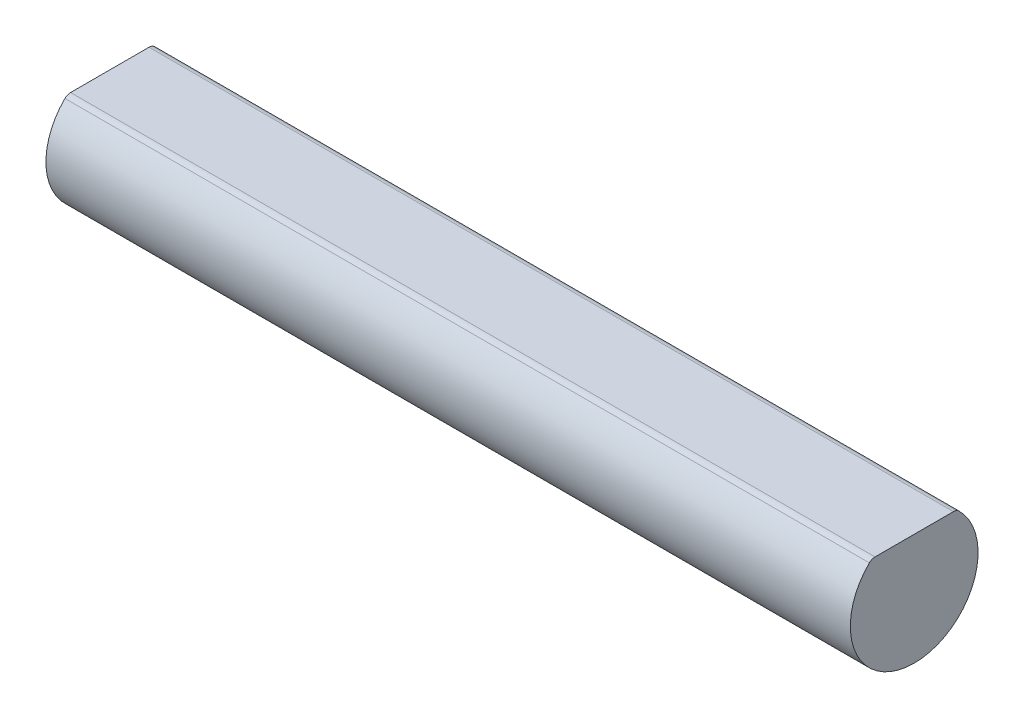
SolidWorks part; units mm, degrees
ref_plane "Front Plane" through (0, 0, 0) normal (0, 0, 1) x (1, 0, 0)
ref_plane "Top Plane" through (0, 0, 0) normal (0, 1, 0) x (1, 0, 0)
ref_plane "Right Plane" through (0, 0, 0) normal (1, 0, 0) x (0, 0, -1)
sketch "Sketch1" plane through (0, 0, 0) normal (1, 0, 0) x (0, 0, -1)
  circle A0 centre (0, 0) radius 7.94
  dimension "D1" = 15.88
extrude "Boss-Extrude1" add sketch "Sketch1" along normal blind 100
sketch "Sketch2" plane through (100, 0, 0) normal (1, 0, 0) x (0, 0, -1)
  line L0 (0, 8.734) -> (0, -8.734) construction
  line L2 (0, 5.94) -> (-10.6918, 5.94)
  line L3 (0, 5.94) -> (0, 9.217)
  line L4 (0, 9.217) -> (-10.6918, 9.217)
  line L5 (-10.6918, 5.94) -> (-10.6918, 9.217)
  line L6 (0, 5.94) -> (8.9119, 5.94)
  line L7 (0, 5.94) -> (0, 9.217)
  line L8 (0, 9.217) -> (8.9119, 9.217)
  line L9 (8.9119, 5.94) -> (8.9119, 9.217)
  circle A0 centre (0, 0) radius 7.94 construction
  point P0 (0, 7.94)
  point P1 (0, 5.94)
  circle M1 centre (0, 0) radius 7.94
  dimension "D1" = 2
extrude "Cut-Extrude1" cut sketch "Sketch2" against normal through all contours L2 L3 M1 | L3 L6 M1 | L6 L9 L8 L3 M1 | L5 L2 L3 L4 M1
fillet "Fillet1" radius 1 2 edges at (50, 5.94, -5.2688) (50, 5.94, 5.2688)
